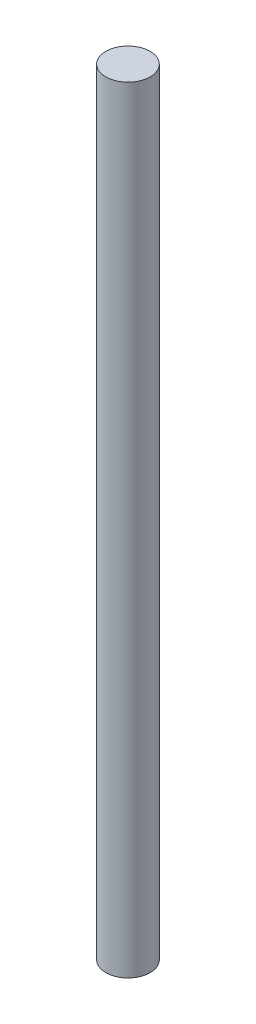
SolidWorks part; units mm, degrees
ref_plane "Front Plane" through (0, 0, 0) normal (0, 0, 1) x (1, 0, 0)
ref_plane "Top Plane" through (0, 0, 0) normal (0, 1, 0) x (1, 0, 0)
ref_plane "Right Plane" through (0, 0, 0) normal (1, 0, 0) x (0, 0, -1)
sketch "Sketch1" plane through (0, 0, 0) normal (0, 1, 0) x (1, 0, 0)
  circle A0 centre (0, 0) radius 1
  dimension "D1" = 2
extrude "Boss-Extrude1" add sketch "Sketch1" along normal mid plane 35
